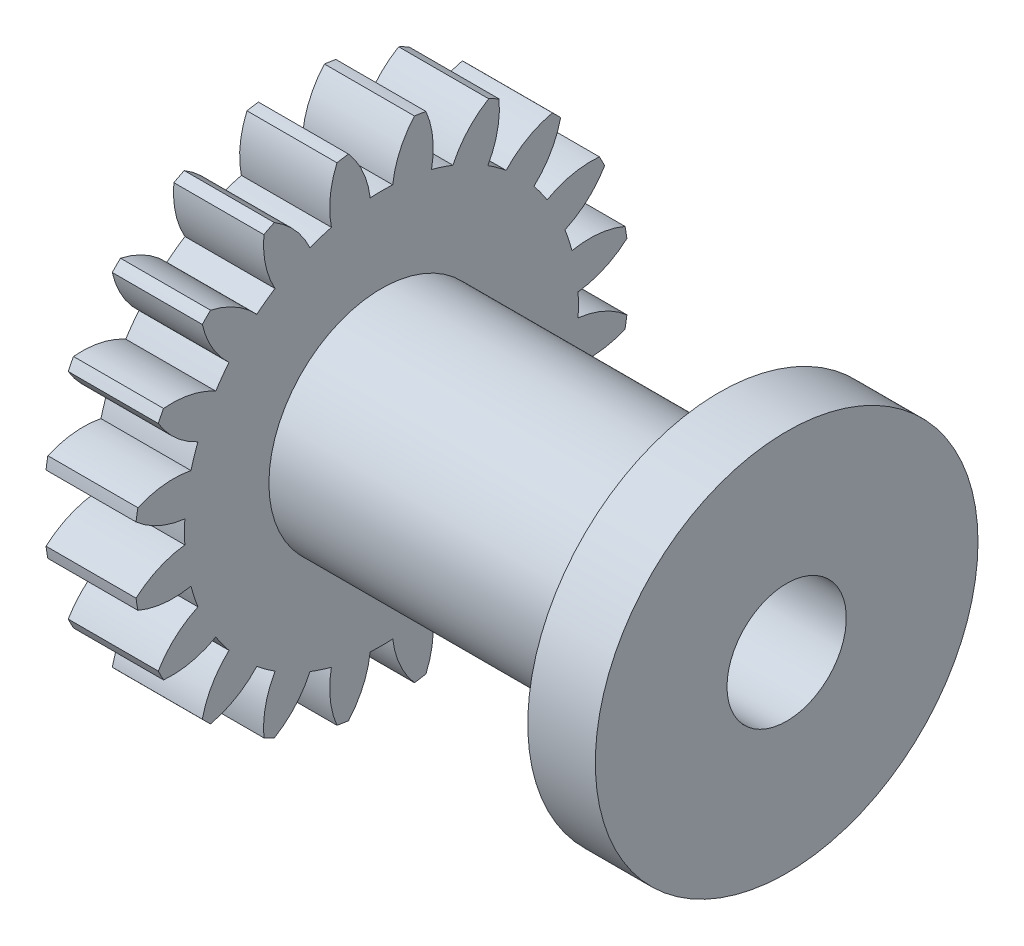
SolidWorks part; units mm, degrees
ref_plane "Plane1" through (0, 0, 0) normal (0, 0, 1) x (1, 0, 0)
ref_plane "Plane2" through (0, 0, 0) normal (0, 1, 0) x (1, 0, 0)
ref_plane "Plane3" through (0, 0, 0) normal (1, 0, 0) x (0, 0, -1)
other "Configuration Table"
sketch "HoldingSke" plane through (0, 0, 0) normal (0, 1, 0) x (1, 0, 0)
  line L0 (0, 0) -> (0.9397, -0.342)
  line L1 (-15, 0) -> (100, 0) construction
  line L2 (0, 0) -> (-2.1039, 2.3779)
  line L3 (0, 0) -> (-11.863, 4.5341)
  line L4 (0, 0) -> (8.1152, 2.9537)
  line L5 (0, 0) -> (-46.8476, -17.4728)
  line L6 (0, 0) -> (-3.3159, -2.2372)
  line L7 (-2.1039, 2.3779) -> (8.6586, 51.2059)
  line L8 (-76.2, 54.61) -> (-75.3, 54.61)
  line L9 (-71.009, 38.7566) -> (-53.1078, 45.2721)
  line L10 (-76.2, 71.12) -> (104.1128, 71.12)
  line L11 (0, 0) -> (-4, 0)
  line L12 (-76.2, 101.6) -> (-76.162, 101.6)
  line L13 (24.9733, 27.94) -> (52.9518, 28.4284)
  line L14 (24.9733, 27.94) -> (24.9743, 27.94)
  line L15 (24.9733, 27.94) -> (100.4006, 29.5858)
  line L16 (-63.627, -1) -> (-12.827, -1)
  circle A0 centre (0, 0) radius 2.5
  circle A1 centre (0, 0) radius 8.749
  circle A2 centre (0, 0) radius 37.5
  circle A3 centre (0, 0) radius 2.5
  dimension "MHD" = 17.498
  dimension "Hub_dia" = 75
  dimension "Bore" = 5
  dimension "MBD" = 5
  dimension "Num_teeth" = 20
  dimension "Pitch" = 1
  dimension "Overall_len" = 50
  dimension "Show_teeth" = 20
  dimension "Thickness" = 4
  dimension "OAL" = 50.0001
  dimension "T_dim" = 0.9
  dimension "Ap" = 20
  dimension "H" = 19.05
  dimension "Pitch_radius" = 180.3128
  dimension "Width" = 4
  dimension "Backlash" = 0.038
  dimension "Addendum_fac" = 1
  dimension "Dedendum_fac" = 1.25
  dimension "Clearance_fac" = 0.25
  dimension "Dedendum_add" = 0.001
  dimension "Module" = 1
sketch "BasProSke" plane through (0, 0, 0) normal (0, 1, 0) x (1, 0, 0)
  line L0 (-10, 0) -> (60, 0) construction
  line L1 (0, 0) -> (0, 11)
  line L2 (0, 0) -> (4, 0)
  line L3 (4, 0) -> (4, 11)
  line L4 (4, 11) -> (0, 11)
  dimension "Thickness" = 4
  dimension "Diameter" = 22
revolve "Base-Revolve" add sketch "BasProSke" angle 360 about L0
sketch "TooCutSke" plane through (0, 0, 0) normal (1, 0, 0) x (0, 0, -1)
  line L1 (0, 0) -> (0, 107) construction
  line L2 (0, 0) -> (-0.8511, 9.9637) construction
  line L3 (0, 0) -> (-3.1206, 19.7028) construction
  line L4 (-0.8511, 9.9637) -> (-1.5603, 9.8514) construction
  arc A0 (0.4999, 8.7347) -> (-0.4999, 8.7347) centre (0, 0) ccw
  arc A1 (1.4852, 10.9249) -> (-1.4852, 10.9249) centre (0, 0) ccw
  circle A2 centre (0, 0) radius 10 construction
  circle A3 centre (0, 0) radius 9.3969 construction
  arc A4 (-0.4999, 8.7347) -> (-1.4852, 10.9249) centre (-4.4722, 8.2645) ccw
  arc A5 (1.4852, 10.9249) -> (0.4999, 8.7347) centre (4.4722, 8.2645) ccw
  dimension "Root_dia" = 17.498
  dimension "Overcut_dia" = 22.0508
  dimension "Pitch_dia" = 20
  dimension "Base_dia" = 18.7939
  dimension "Flank_rad" = 4
  dimension "Half_ang" = 9
  dimension "Half_CT" = 0.7181
extrude "ToothCut" cut sketch "TooCutSke" along normal through all
fillet "Breaks" [suppressed] radius 0.02
fillet "RootFillets" [suppressed] radius 0.251
pattern_circular "TeethCuts" count 20 every 18 about axis through (-10, 0, 0) along (1, 0, 0) of "ToothCut", "RootFillets", "Breaks"
sketch "HubNeaOneSke" plane through (0, 0, 0) normal (-1, 0, 0) x (0, 0, 1)
  circle A0 centre (0, 0) radius 8.749
  dimension "Diameter" = 17.498
extrude "HubNearOne" [suppressed] add sketch "HubNeaOneSke" along normal blind 46.0001
sketch "HubNeaBotSke" plane through (0, 0, 0) normal (-1, 0, 0) x (0, 0, 1)
  circle A0 centre (0, 0) radius 8.749
  dimension "Diameter" = 17.498
extrude "HubNearBoth" [suppressed] add sketch "HubNeaBotSke" along normal blind 23
ref_plane "FarPln" through (4, 0, 0) normal (1, 0, 0) x (0, 0, -1)
sketch "HubFarSke" plane through (4, 0, 0) normal (1, 0, 0) x (0, 0, -1)
  circle A0 centre (0, 0) radius 8.749
  dimension "Diameter" = 17.498
extrude "HubFar" [suppressed] add sketch "HubFarSke" along normal blind 23
sketch "BorSke" plane through (0, 0, 0) normal (1, 0, 0) x (0, 0, -1)
  circle A0 centre (0, 0) radius 2.5
  dimension "Diameter" = 5
extrude "Bore" cut sketch "BorSke" along normal mid plane 100.0001
sketch "KeySke" plane through (0, 0, 0) normal (1, 0, 0) x (0, 0, -1)
  line L0 (-1, 0) -> (-1, 3.4)
  line L1 (-1, 3.4) -> (1, 3.4)
  line L2 (1, 3.4) -> (1, 0)
  line L3 (0, 0) -> (0, 34) construction
  line L4 (-1, 0) -> (1, 0)
  dimension "Offset" = 3.4
  dimension "Width" = 2
extrude "Keyway" [suppressed] cut sketch "KeySke" along normal mid plane 100.0001
pattern_circular "Keyway2" [suppressed] count 2 every 90 about axis through (-10, 0, 0) along (1, 0, 0)
sketch "Sketch1" plane through (4, 0, 0) normal (1, 0, 0) x (0, 0, -1)
  circle A0 centre (0, 0) radius 8.5
  dimension "D1" = 17
extrude "Boss-Extrude1" [suppressed] add sketch "Sketch1" along normal blind 4
sketch "Sketch2" plane through (4, 0, 0) normal (1, 0, 0) x (0, 0, -1)
  circle A0 centre (0, 0) radius 5
  dimension "D1" = 10
extrude "Boss-Extrude2" add sketch "Sketch2" along normal blind 15
sketch "Sketch3" plane through (19, 0, 0) normal (1, 0, 0) x (0, 0, -1)
  circle A0 centre (0, 0) radius 8.5
extrude "Boss-Extrude3" add sketch "Sketch3" along normal blind 3
sketch "Sketch4" plane through (22, 0, 0) normal (1, 0, 0) x (0, 0, -1)
  circle A0 centre (0, 0) radius 2.65
  dimension "D1" = 5.3
extrude "Cut-Extrude1" cut sketch "Sketch4" along normal through all both and the other way through all
equation "' \"Module@HoldingSke\" = 6.35"
equation "' \"Num_teeth@HoldingSke\" = 12"
equation "' \"Ap@HoldingSke\" =  20"
equation "' \"Ap@HoldingSke\" = 20"
equation "' \"Width@HoldingSke\" = 0.5 * 25.4"
equation "' \"Hub_dia@HoldingSke\"= 1 * 25.4"
equation "' \"Hub_dia@HoldingSke\" = 1 * 25.4"
equation "' \"Overall_len@HoldingSke\" = 1.0 * 25.4"
equation "' \"Bore@HoldingSke\" = 0.75 * 25.4"
equation "' \"T_dim@HoldingSke\" = 0.1 * 25.4"
equation "' \"Width@KeySke\" = 0.25 * 25.4"
equation "' \"Show_teeth@HoldingSke\" = 13"
equation "' \"Backlash@HoldingSke\" = 0.009 * 25.4"
equation "' \"Addendum_fac@HoldingSke\" = 1.0"
equation "' \"Dedendum_fac@HoldingSke\" = 1.25"
equation "' \"Dedendum_add@HoldingSke\" = 0.00005 * 25.4"
equation "' \"Clearance_fac@HoldingSke\" = 0.25"
equation "\"Pitch@HoldingSke\" = 1 / \"Module@HoldingSke\""
equation "\"Overcut_dia@TooCutSke\" = (\"Num_teeth@HoldingSke\" + 2 * \"Addendum_fac@HoldingSke\") / \"Pitch@HoldingSke\" + 0.002 * 25.4"
equation "\"Pitch_dia@TooCutSke\" = \"Num_teeth@HoldingSke\" / \"Pitch@HoldingSke\""
equation "\"Base_dia@TooCutSke\" = \"Num_teeth@HoldingSke\" / \"Pitch@HoldingSke\" * cos((\"Ap@HoldingSke\"  * 3.14159265 / 180))"
equation "\"Root_dia@TooCutSke\" = (\"Num_teeth@HoldingSke\" + 2) / \"Pitch@HoldingSke\" - 2 * (\"Addendum_fac@HoldingSke\" + \"Dedendum_fac@HoldingSke\") / \"Pitch@HoldingSke\" - \"Dedendum_add@HoldingSke\" * 2"
equation "\"Half_ang@TooCutSke\" = 180 / \"Num_teeth@HoldingSke\""
equation "\"Half_CT@TooCutSke\" = \"Num_teeth@HoldingSke\" / \"Pitch@HoldingSke\" * sin((3.14159265 / 2 / \"Num_teeth@HoldingSke\")) / 2 - 7 * \"Backlash@HoldingSke\" / 4"
equation "\"Flank_rad@TooCutSke\" = \"Num_teeth@HoldingSke\" / \"Pitch@HoldingSke\" / 5"
equation "\"Radius@RootFillets\" = \"Clearance_fac@HoldingSke\" / \"Pitch@HoldingSke\" + \"Dedendum_add@HoldingSke\""
equation "\"Break_rad@Breaks\" = 0.02 / \"Pitch@HoldingSke\""
equation "\"Thickness@HoldingSke\" = \"Width@HoldingSke\""
equation "\"OAL@HoldingSke\" = \"Thickness@HoldingSke\""
equation "\"MHD@HoldingSke\" = (\"Num_teeth@HoldingSke\" + 2) / \"Pitch@HoldingSke\" - 2 * (\"Addendum_fac@HoldingSke\" + \"Dedendum_fac@HoldingSke\")  / \"Pitch@HoldingSke\" - \"Dedendum_add@HoldingSke\" * 2"
equation "\"MBD@HoldingSke\" = (\"Num_teeth@HoldingSke\" + 2) / \"Pitch@HoldingSke\" - 2 * (\"Addendum_fac@HoldingSke\" + \"Dedendum_fac@HoldingSke\")  / \"Pitch@HoldingSke\" - \"Dedendum_add@HoldingSke\" * 2 - 0.002 * 25.4"
equation "\"MHD@HoldingSke\" = ((sgn( \"MHD@HoldingSke\" - \"Hub_dia@HoldingSke\" )-1)*( \"MHD@HoldingSke\" - \"Hub_dia@HoldingSke\" ))/-2+ \"Hub_dia@HoldingSke\""
equation "\"MBD@HoldingSke\" = ((sgn( \"MBD@HoldingSke\" - \"Bore@HoldingSke\" )-1)*( \"MBD@HoldingSke\" - \"Bore@HoldingSke\" ))/-2+ \"Bore@HoldingSke\""
equation "\"OAL@HoldingSke\" = ((sgn( \"OAL@HoldingSke\" - \"Overall_len@HoldingSke\" )+1)*( \"OAL@HoldingSke\" - \"Overall_len@HoldingSke\" ))/2 + \"Overall_len@HoldingSke\" + 0.000002 * 25.4"
equation "\"Num_teeth@TeethCuts\" = int( \"Show_teeth@HoldingSke\" ) + 1"
equation "\"Num_teeth@TeethCuts\" = ((sgn( \"Num_teeth@TeethCuts\" - \"Num_teeth@HoldingSke\" )-1)*( \"Num_teeth@TeethCuts\" - \"Num_teeth@HoldingSke\" ))/-2+ \"Num_teeth@HoldingSke\""
equation "\"Num_teeth@TeethCuts\" = ((sgn( \"Num_teeth@TeethCuts\" - 2.0)+1)*( \"Num_teeth@TeethCuts\" - 2.0))/2 +2.0"
equation "\"Angle@TeethCuts\" = 360.0 / \"Num_teeth@HoldingSke\""
equation "\"Diameter@BasProSke\" = (\"Num_teeth@HoldingSke\" + 2 * \"Addendum_fac@HoldingSke\") / \"Pitch@HoldingSke\""
equation "\"Thickness@BasProSke\"  = \"Thickness@HoldingSke\""
equation "' \"Fillet_rad@BasProSke\" =  \"Thickness@HoldingSke\" * 0.05"
equation "' \"Fillet_rad@BasProSke\" = \"Thickness@HoldingSke\" * 0.05"
equation "\"MHD@HoldingSke\" = ((sgn( \"MHD@HoldingSke\" - \"Root_dia@TooCutSke\" )-1)*( \"MHD@HoldingSke\" - \"Root_dia@TooCutSke\" ))/-2+ \"Root_dia@TooCutSke\""
equation "\"Diameter@HubNeaOneSke\" = \"MHD@HoldingSke\""
equation "\"Length@HubNearOne\" = \"OAL@HoldingSke\" - \"Thickness@BasProSke\""
equation "\"Diameter@HubNeaBotSke\" = \"MHD@HoldingSke\""
equation "\"Length@HubNearBoth\" = ( \"OAL@HoldingSke\" - \"Thickness@BasProSke\" ) / 2.0"
equation "\"Thickness@FarPln\" = \"Thickness@BasProSke\""
equation "\"Diameter@HubFarSke\" = \"MHD@HoldingSke\""
equation "\"Length@HubFar\" = ( \"OAL@HoldingSke\" - \"Thickness@BasProSke\" ) / 2.0"
equation "\"Diameter@BorSke\" = \"MBD@HoldingSke\""
equation "\"D1@Bore\" = \"OAL@HoldingSke\" * 2.0"
equation "\"D1@Keyway\" = \"OAL@HoldingSke\" * 2.0"
equation "\"Offset@KeySke\" = \"T_dim@HoldingSke\" + \"MBD@HoldingSke\" / 2.0"
